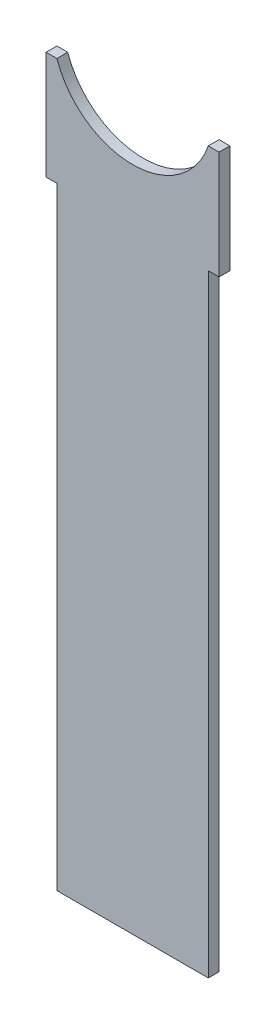
SolidWorks part; units mm, degrees
material "AISI 4130 Steel, annealed at 865C"
ref_plane "X-Y Datum" through (0, 0, 0) normal (0, 0, 1) x (1, 0, 0)
ref_plane "X-Z Datum" through (0, 0, 0) normal (0, 1, 0) x (1, 0, 0)
ref_plane "Y-Z Datum" through (0, 0, 0) normal (1, 0, 0) x (0, 0, -1)
sketch "Sketch2" plane through (0, 0, 0) normal (0, 0, 1) x (1, 0, 0)
  line L0 (-12.7, -7.9375) -> (12.7, -7.9375) construction
  line L2 (-11.1125, 0) -> (-11.1125, -105.8046)
  line L3 (-11.1125, -105.8046) -> (11.1125, -105.8046)
  line L4 (11.1125, 0) -> (11.1125, -105.8046)
  line L5 (-11.1125, -15.875) -> (-12.7, -15.875)
  line L6 (-11.1125, -15.875) -> (-11.1125, 0)
  line L7 (-11.1125, 0) -> (-12.7, 0)
  line L8 (-12.7, -15.875) -> (-12.7, 0)
  line L9 (11.1125, -15.875) -> (12.7, -15.875)
  line L10 (11.1125, -15.875) -> (11.1125, 0)
  line L11 (11.1125, 0) -> (12.7, 0)
  line L12 (12.7, -15.875) -> (12.7, 0)
  line L13 (-11.1125, -105.8046) -> (-12.7, -105.8046) construction
  arc A1 (-11.1125, 0) -> (11.1125, 0) centre (0, 3.81) ccw
  point P0 (0, -105.8046)
  dimension "D1" = 1.5875
  dimension "D2" = 25.4
  dimension "D4" = 15.875
extrude "Boss-Extrude1" add sketch "Sketch2" along normal blind 1.5875 contours L0 L6 L2 L3 L4 L10 | A1 L0 L4 | L4 L0 L12 L11 | L0 L10 L9 L12 | L0 L8 L5 L6 | L8 L0 L2 L7 | L2 L0 A1
